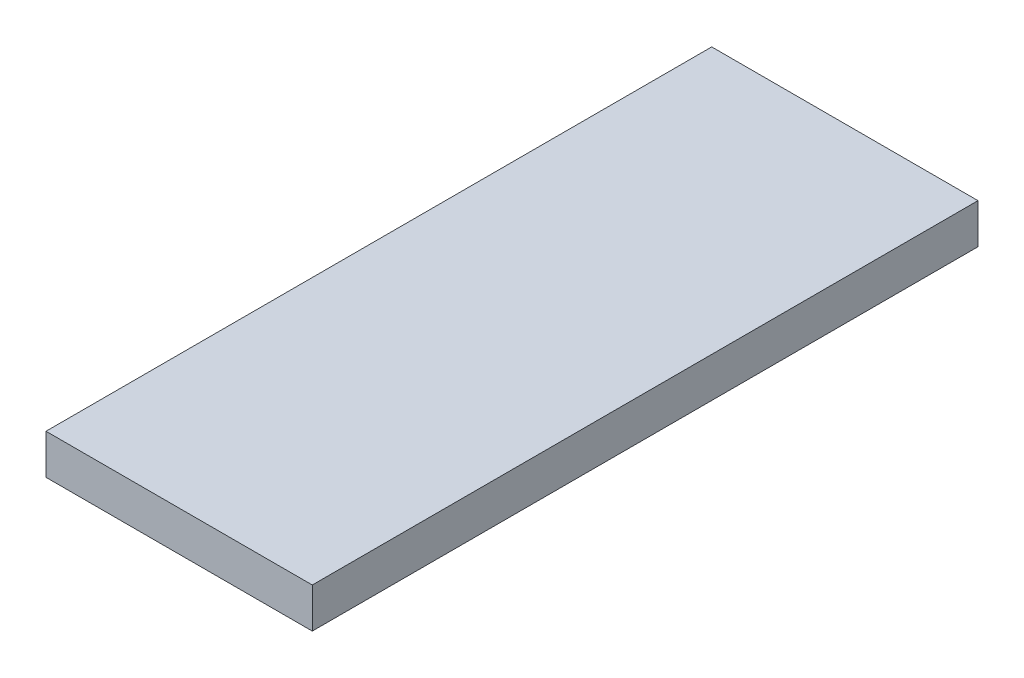
SolidWorks part; units mm, degrees
ref_plane "Front Plane" through (0, 0, 0) normal (0, 0, 1) x (1, 0, 0)
ref_plane "Top Plane" through (0, 0, 0) normal (0, 1, 0) x (1, 0, 0)
ref_plane "Right Plane" through (0, 0, 0) normal (1, 0, 0) x (0, 0, -1)
sketch "Sketch1" plane through (0, 0, 0) normal (0, 1, 0) x (1, 0, 0)
  line L1 (0, 0) -> (50.8, 0)
  line L2 (0, 0) -> (0, 127)
  line L3 (0, 127) -> (50.8, 127)
  line L4 (50.8, 0) -> (50.8, 127)
  dimension "D1" = 50.8
  dimension "D2" = 127
extrude "Boss-Extrude1" add sketch "Sketch1" along normal blind 7.62
